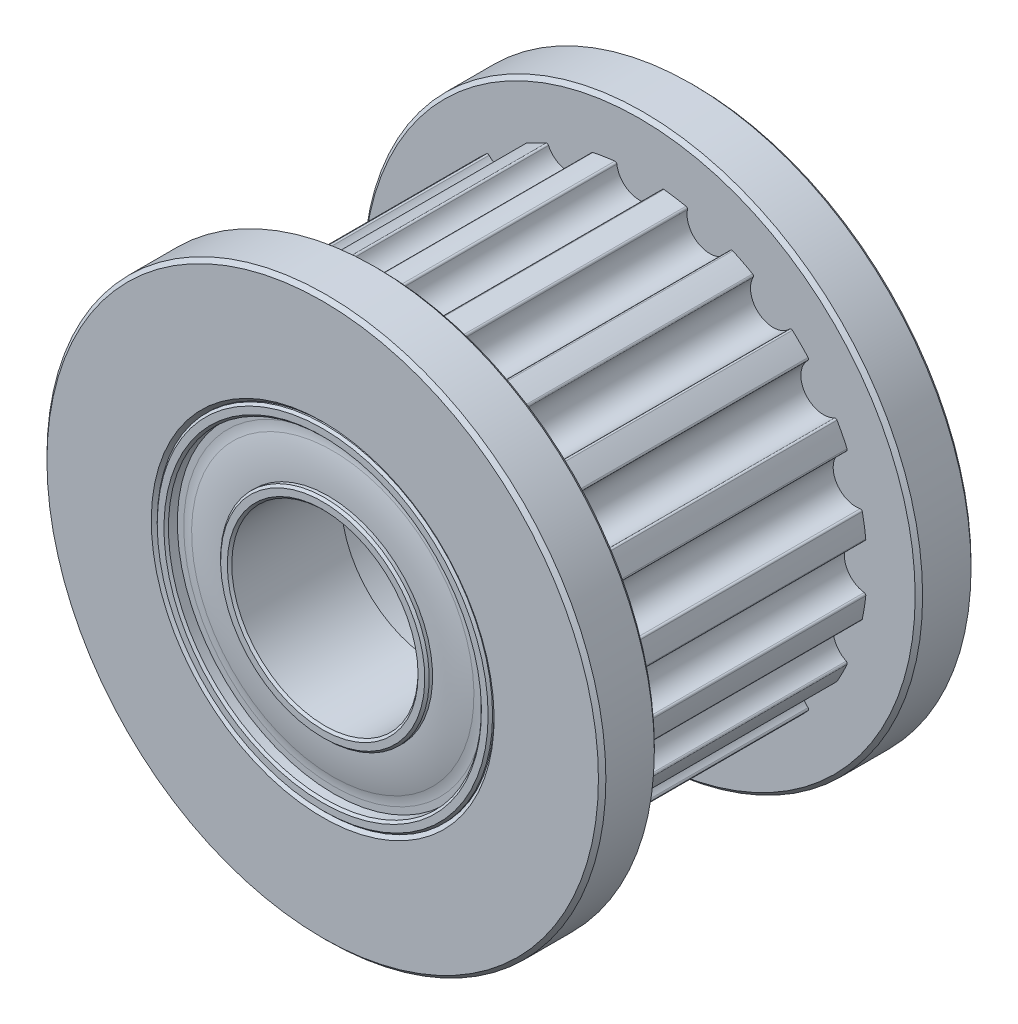
SolidWorks part; units mm, degrees
ref_plane "Front" through (0, 0, 0) normal (0, 0, 1) x (1, 0, 0)
ref_plane "Top" through (0, 0, 0) normal (0, 1, 0) x (1, 0, 0)
ref_plane "Right" through (0, 0, 0) normal (1, 0, 0) x (0, 0, -1)
sketch "Sketch1" plane through (0, 0, 0) normal (1, 0, 0) x (0, 0, -1)
  line L0 (-5, 0) -> (5, 0) construction
  line L1 (5, 7.5) -> (5, -7.5) construction
  line L2 (5, 7.5) -> (3.5, 7.5) construction
  line L3 (5, 2.5) -> (5, -2.5) construction
  line L4 (5, 6.11) -> (5, -6.11) construction
  line L5 (3, 0) -> (-3, 0) construction
  line L6 (3.5, 7.5) -> (3.5, 6.11) construction
  line L7 (5, 4.5) -> (2, 4.5) construction
  line L8 (2, 4.5) -> (2, 2.5) construction
  line L9 (2, 2.5) -> (5, 2.5) construction
  line L10 (5, 4.5) -> (5, -4.5) construction
  line L11 (-5, 0) -> (-5, 7.5) construction
  line L12 (-5, 7.5) -> (-3.5, 7.5) construction
  line L13 (-3.5, 7.5) -> (-3.5, 6.11) construction
  line L14 (-3.5, 6.11) -> (3.5, 6.11) construction
  line L15 (3.5, 6.11) -> (3.5, -6.11) construction
  line L16 (3.5, -6.11) -> (-3.5, -6.11) construction
  line L17 (-3.5, -6.11) -> (-3.5, 6.11) construction
  line L18 (0, -3.5) -> (0, 3.5) construction
  point P15 (5, 0)
  point P22 (3.5, 0)
  point P24 (-3, -6.11)
  point P25 (3, -6.11)
  point P29 (0, 0)
  dimension "Width" = 10
  dimension "OD" = 15
  dimension "ID" = 5
  dimension "Diameter" = 12.22
  dimension "Groove Depth" = 1.39
  dimension "For Maximum Belt Width" = 6
  dimension "For Shaft Diameter" = 5
  dimension "Bearing Diameter" = 9
  dimension "Bearing Width" = 3
  dimension "Inside Width" = 7
  dimension "Wall Thickness" = 1.5
  dimension "D1" = 7
sketch "Sketch5" plane through (0, 0, 0) normal (0, 0, 1) x (1, 0, 0)
  circle A0 centre (0, 0) radius 7.5 construction
  circle A1 centre (0, 0) radius 6.11 construction
  circle A2 centre (0, 0) radius 2.5 construction
  point P5 (0, 0)
  point P9 (-6.11, 0)
  point P10 (-7.5, 0)
  point P13 (0, 6.11)
sketch "Sketch2" plane through (0, 0, 0) normal (1, 0, 0) x (0, 0, -1)
  line L0 (5, 2.5) -> (2, 2.5)
  line L1 (5, 2.5) -> (5, 2.8)
  line L2 (5, 7.5) -> (5, -7.5) construction
  line L3 (5, 2.8) -> (4.7, 2.8) construction
  line L4 (4.85, 4.2) -> (4.85, 2.8) construction
  line L5 (5, 4.5) -> (2, 4.5)
  line L6 (4.7, 3.9) -> (4.7, 4.2)
  line L7 (5, 4.5) -> (5, 4.2)
  line L8 (5, 4.2) -> (4.7, 4.2)
  line L9 (4.7, 4.2) -> (4.7, 2.8) construction
  line L10 (2, 4.5) -> (2, 2.5)
  line L11 (4.85, 2.8) -> (5, 2.8)
  arc A0 (4.7, 3.9) -> (4.85, 2.8) centre (0.7417, 2.8) cw
  dimension "D1" = 0.3
revolve "Revolve1" add sketch "Sketch2" angle 360 about L0
chamfer "Chamfer2" distance 0.06 angle 45 4 edges at (0, -2.8, -5) (0, -2.5, -5) (0, -4.2, -5) (0, -4.5, -5)
fillet "Fillet2" radius 1 1 edges at (0, -3.9, -4.7)
mirror "Mirror1" about plane through (0, 0, 0) normal (0, 0, 1) of bodies 108
sketch "Sketch3" plane through (0, 0, 0) normal (1, 0, 0) x (0, 0, -1)
  line L0 (3.5, 7.5) -> (5, 7.5)
  line L1 (5, 7.5) -> (5, 4.5)
  line L2 (5, 7.5) -> (5, -7.5) construction
  line L3 (-5, 4.5) -> (-2, 4.5)
  line L4 (-2, 4.5) -> (-2, 3.5)
  line L5 (-2, 3.5) -> (2, 3.5)
  line L6 (2, 3.5) -> (2, 4.5)
  line L8 (2, 4.5) -> (5, 4.5)
  line L9 (3.5, 7.5) -> (3.5, 6.11)
  line L10 (3.5, 6.11) -> (-3.5, 6.11)
  line L11 (0, 6.11) -> (0, 4.5) construction
  line L12 (-5, 4.5) -> (5, 4.5) construction
  line L13 (-3.5, 7.5) -> (-3.5, 6.11)
  line L19 (-5, 7.5) -> (-5, 4.5)
  line L20 (-3.5, 7.5) -> (-5, 7.5)
revolve "Revolve2" add sketch "Sketch3" angle 360 about L0
chamfer "Chamfer1" distance 0.1 angle 45 6 edges at (0, -7.5, -5) (0, -7.5, -3.5) (0, -7.5, 3.5) (0, -7.5, 5) (0, -4.5, -5) (0, -4.5, 5)
sketch "Sketch4" plane through (0, 0, 0) normal (0, 0, 1) x (1, 0, 0)
  line L0 (-0.611, 6.11) -> (0.611, 6.11)
  line L1 (-0.611, 6.11) -> (-0.611, 5.554) construction
  line L2 (-0.611, 5.554) -> (0.611, 5.554) construction
  line L3 (0.611, 5.554) -> (0.611, 6.11) construction
  line L4 (0, 6.11) -> (0, 5.554) construction
  arc A0 (0.611, 6.11) -> (-0.611, 6.11) centre (0, 6.11) cw
  dimension "D1" = 0.556
  dimension "D3" = 1.222
extrude "Cut-Extrude1" cut sketch "Sketch4" against normal up to surface (3.5 mm away) and the other way up to surface (3.5 mm away)
fillet "Fillet1" radius 0.05 2 edges at (-0.6102, 6.0795, 0) (0.6102, 6.0795, 0)
pattern_circular "CirPattern3" count 20 over 360 about axis through (0, 0, 0) along (0, 0, 1) of "Cut-Extrude1", "Fillet1"
equation "\"D1@Sketch4\"=\"Groove Depth@Sketch1\"/2.5"
equation "\"D3@Sketch4\"=\"Diameter@Sketch1\"/10"
equation "\"D1@Sketch1\"=\"ID@Sketch1\"+2"
